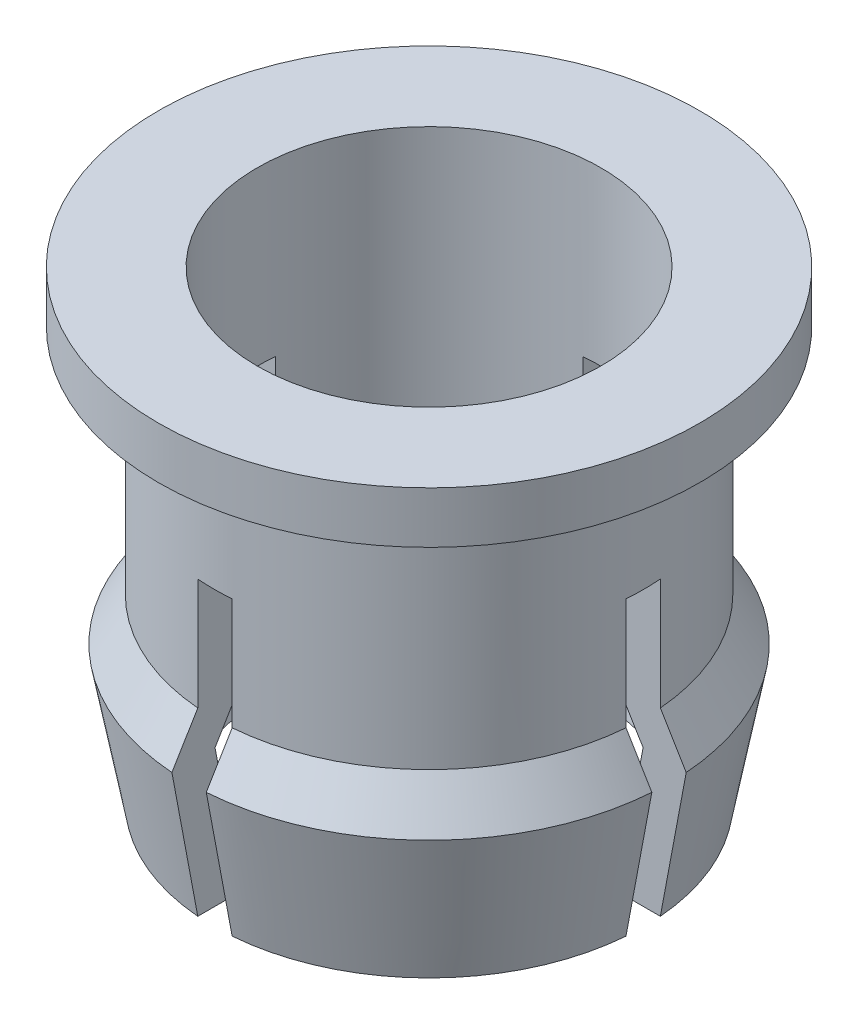
SolidWorks part; units mm, degrees
ref_plane "Front" through (0, 0, 0) normal (0, 0, 1) x (1, 0, 0)
ref_plane "Top" through (0, 0, 0) normal (0, 1, 0) x (1, 0, 0)
ref_plane "Right" through (0, 0, 0) normal (1, 0, 0) x (0, 0, -1)
sketch "Sketch1" plane through (0, 0, 0) normal (0, 1, 0) x (1, 0, 0)
  circle A0 centre (0, 0) radius 4.0005
  circle A1 centre (0, 0) radius 2.54
  dimension "D1" = 8.001
  dimension "D2" = 5.08
extrude "Extrude1" add sketch "Sketch1" against normal blind 0.762
sketch "Sketch2" plane through (0, -0.762, 0) normal (0, -1, 0) x (1, 0, 0)
  circle A0 centre (0, 0) radius 2.54 construction
  circle A1 centre (0, 0) radius 2.54
  circle A2 centre (0, 0) radius 3.175
  dimension "D1" = 6.35
extrude "Extrude2" add sketch "Sketch2" along normal blind 3.429
sketch "Sketch3" plane through (0, 0, 0) normal (1, 0, 0) x (0, 0, -1)
  line L0 (0, 1.2149) -> (0, -8.1089) construction
  line L1 (-3.175, -4.191) -> (3.175, -4.191) construction
  line L2 (-3.175, -4.191) -> (-2.54, -4.191)
  line L3 (-3.175, -4.191) -> (-3.556, -4.826)
  line L4 (-3.556, -4.826) -> (-3.175, -6.858)
  line L5 (-3.175, -6.858) -> (-2.54, -6.858)
  line L6 (-2.54, -6.858) -> (-2.921, -4.826)
  line L7 (-2.921, -4.826) -> (-2.54, -4.191)
  line L8 (-2.54, 0) -> (-2.54, -4.191) construction
  dimension "D1" = 2.667
  dimension "D2" = 3.556
  dimension "D3" = 2.032
revolve "Revolve1" add sketch "Sketch3" angle 360 about L0
ref_plane "Plane1" through (0, -2.54, 0) normal (0, -1, 0) x (1, 0, 0)
sketch "Sketch5" plane through (0, -2.54, 0) normal (0, -1, 0) x (1, 0, 0)
  line L0 (-0.254, 0.254) -> (-4.064, 0.254)
  line L1 (4.064, 0.254) -> (0.254, 0.254)
  line L2 (4.064, 0.254) -> (4.064, -0.254)
  line L3 (4.064, -0.254) -> (0.254, -0.254)
  line L4 (-4.064, 0.254) -> (-4.064, -0.254)
  line L5 (0.254, 4.064) -> (-0.254, 4.064)
  line L6 (0.254, 4.064) -> (0.254, 0.254)
  line L7 (0.254, -4.064) -> (-0.254, -4.064)
  line L8 (-0.254, 4.064) -> (-0.254, 0.254)
  line L9 (0.254, -0.254) -> (0.254, -4.064)
  line L10 (-0.254, -0.254) -> (-4.064, -0.254)
  line L11 (-0.254, -0.254) -> (-0.254, -4.064)
  dimension "D1" = 0.508
  dimension "D2" = 0.508
  dimension "D3" = 0.254
  dimension "D4" = 0.254
  dimension "D5" = 3.81
  dimension "D6" = 3.81
  dimension "D7" = 3.81
  dimension "D8" = 3.81
extrude "Cut-Extrude1" cut sketch "Sketch5" along normal through all
